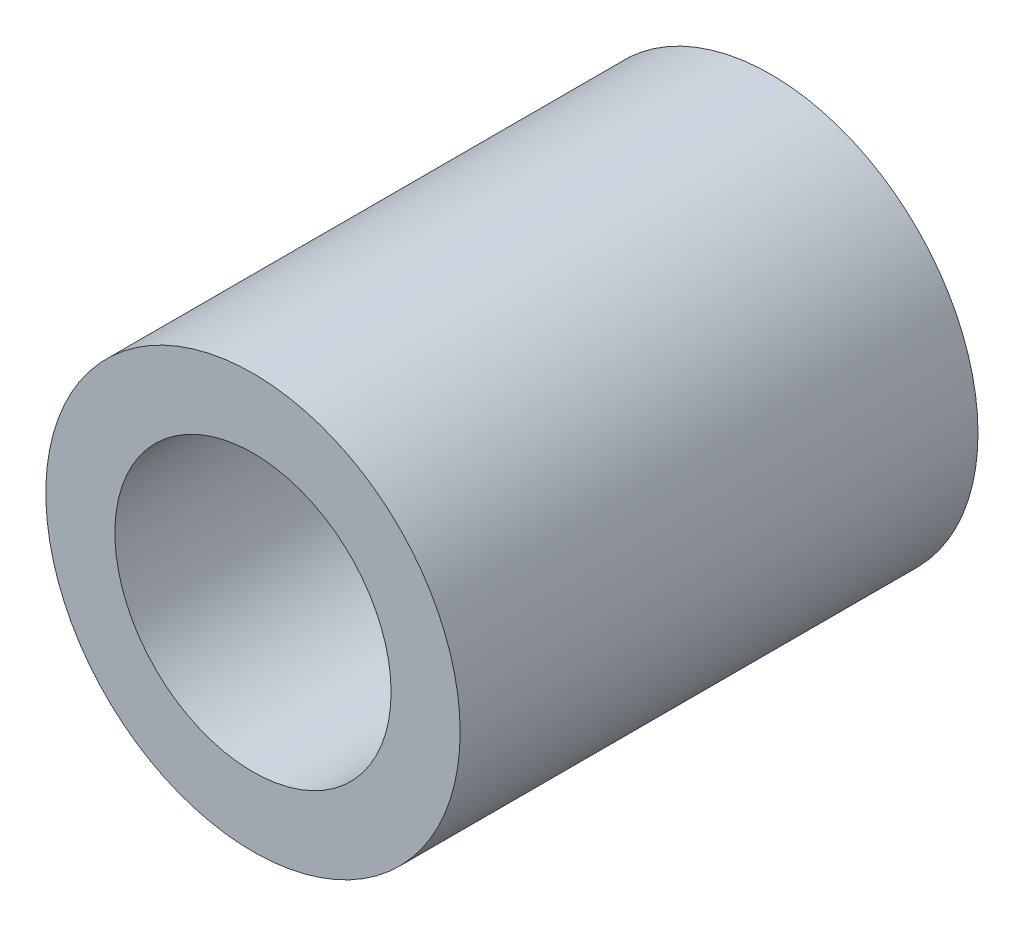
SolidWorks part; units mm, degrees
ref_plane "Front Plane" through (0, 0, 0) normal (0, 0, 1) x (1, 0, 0)
ref_plane "Top Plane" through (0, 0, 0) normal (0, 1, 0) x (1, 0, 0)
ref_plane "Right Plane" through (0, 0, 0) normal (1, 0, 0) x (0, 0, -1)
sketch "Sketch1" plane through (0, 0, 0) normal (0, 0, 1) x (1, 0, 0)
  circle A0 centre (0, 0) radius 1.6
  circle A1 centre (0, 0) radius 2.4
  dimension "D1" = 3.2
  dimension "D2" = 4.8
extrude "Boss-Extrude1" add sketch "Sketch1" along normal blind 6
